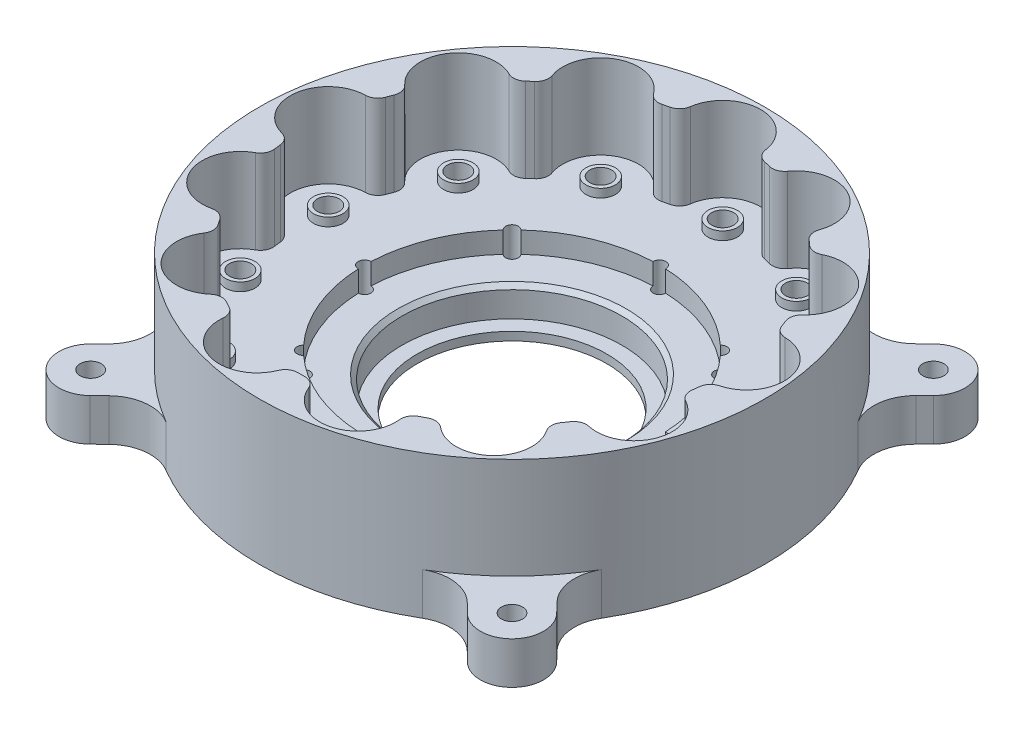
SolidWorks part; units mm, degrees
ref_plane "Front Plane" through (0, 0, 0) normal (0, 0, 1) x (1, 0, 0)
ref_plane "Top Plane" through (0, 0, 0) normal (0, 1, 0) x (1, 0, 0)
ref_plane "Right Plane" through (0, 0, 0) normal (1, 0, 0) x (0, 0, -1)
sketch "Sketch1" plane through (0, 0, 0) normal (0, 1, 0) x (1, 0, 0)
  circle A0 centre (0, 0) radius 60
  dimension "D1" = 120
extrude "Boss-Extrude1" add sketch "Sketch1" along normal blind 9
sketch "Sketch2" plane through (0, 9, 0) normal (0, 1, 0) x (1, 0, 0)
  circle A0 centre (0, 0) radius 26.1
  dimension "D1" = 52.2
extrude "Cut-Extrude1" cut sketch "Sketch2" against normal blind 7
sketch "Sketch3" plane through (0, 2, 0) normal (0, 1, 0) x (1, 0, 0)
  circle A0 centre (0, 0) radius 22.5
  dimension "D1" = 45
extrude "Cut-Extrude2" cut sketch "Sketch3" against normal blind 8
sketch "Sketch7" plane through (0, 9, 0) normal (0, 1, 0) x (1, 0, 0)
  circle A0 centre (0, 0) radius 35
  circle A1 centre (0, 0) radius 60 construction
  circle A2 centre (0, 0) radius 60
  dimension "D1" = 70
extrude "Boss-Extrude4" add sketch "Sketch7" along normal blind 5
sketch "Sketch4" plane through (0, 14, 0) normal (0, 1, 0) x (1, 0, 0)
  circle A0 centre (0, 50) radius 2.5
  circle A1 centre (23.2362, 44.2728) radius 2.5
  circle A2 centre (41.1492, 28.4032) radius 2.5
  circle A3 centre (49.6354, 6.0268) radius 2.5
  circle A4 centre (46.7508, -17.7302) radius 2.5
  circle A5 centre (33.1561, -37.4255) radius 2.5
  circle A6 centre (11.9658, -48.5471) radius 2.5
  circle A7 centre (-11.9658, -48.5471) radius 2.5
  circle A8 centre (-33.1561, -37.4255) radius 2.5
  circle A9 centre (-46.7508, -17.7302) radius 2.5
  circle A10 centre (-49.6354, 6.0268) radius 2.5
  circle A11 centre (-41.1492, 28.4032) radius 2.5
  circle A12 centre (-23.2362, 44.2728) radius 2.5
  point P30 (0, 0)
  dimension "5" = 5
  dimension "D1" = 50
  dimension "D3" = 13
extrude "Cut-Extrude3" cut sketch "Sketch4" against normal through all
sketch "Sketch5" plane through (0, 14, 0) normal (0, 1, 0) x (1, 0, 0)
  circle A0 centre (0, 50) radius 3.5
  circle A1 centre (0, 50) radius 2.5
  circle A2 centre (23.2362, 44.2728) radius 3.5
  circle A3 centre (23.2362, 44.2728) radius 2.5
  circle A4 centre (41.1492, 28.4032) radius 3.5
  circle A5 centre (41.1492, 28.4032) radius 2.5
  circle A6 centre (49.6354, 6.0268) radius 3.5
  circle A7 centre (49.6354, 6.0268) radius 2.5
  circle A8 centre (46.7508, -17.7302) radius 3.5
  circle A9 centre (46.7508, -17.7302) radius 2.5
  circle A10 centre (33.1561, -37.4255) radius 3.5
  circle A11 centre (33.1561, -37.4255) radius 2.5
  circle A12 centre (11.9658, -48.5471) radius 3.5
  circle A13 centre (11.9658, -48.5471) radius 2.5
  circle A14 centre (-11.9658, -48.5471) radius 3.5
  circle A15 centre (-11.9658, -48.5471) radius 2.5
  circle A16 centre (-33.1561, -37.4255) radius 3.5
  circle A17 centre (-33.1561, -37.4255) radius 2.5
  circle A18 centre (-46.7508, -17.7302) radius 3.5
  circle A19 centre (-46.7508, -17.7302) radius 2.5
  circle A20 centre (-49.6354, 6.0268) radius 3.5
  circle A21 centre (-49.6354, 6.0268) radius 2.5
  circle A22 centre (-41.1492, 28.4032) radius 3.5
  circle A23 centre (-41.1492, 28.4032) radius 2.5
  circle A24 centre (-23.2362, 44.2728) radius 3.5
  circle A25 centre (-23.2362, 44.2728) radius 2.5
  point P43 (0, 0)
  dimension "D1" = 7
  dimension "D2" = 5
  dimension "D3" = 13
extrude "Boss-Extrude2" add sketch "Sketch5" along normal blind 2
sketch "Sketch6" plane through (0, 14, 0) normal (0, 1, 0) x (1, 0, 0)
  arc A0 (8.9635, 49.19) -> (-8.9635, 49.19) centre (0, 50) ccw
  arc A2 (14.923, 47.7211) -> (8.9635, 49.19) centre (0, 0) ccw
  arc A3 (30.7965, 39.39) -> (14.923, 47.7211) centre (23.2362, 44.2728) ccw
  arc A4 (35.3907, 35.3199) -> (30.7965, 39.39) centre (0, 0) ccw
  arc A5 (45.5744, 20.5663) -> (35.3907, 35.3199) centre (41.1492, 28.4032) ccw
  arc A6 (47.7509, 14.8273) -> (45.5744, 20.5663) centre (0, 0) ccw
  arc A7 (49.9118, -2.9689) -> (47.7509, 14.8273) centre (49.6354, 6.0268) ccw
  arc A8 (49.1719, -9.062) -> (49.9118, -2.9689) centre (0, 0) ccw
  arc A9 (42.815, -25.824) -> (49.1719, -9.062) centre (46.7508, -17.7302) ccw
  arc A10 (39.3283, -30.8754) -> (42.815, -25.824) centre (0, 0) ccw
  arc A11 (25.9097, -42.7631) -> (39.3283, -30.8754) centre (33.1561, -37.4255) ccw
  arc A12 (20.475, -45.6155) -> (25.9097, -42.7631) centre (0, 0) ccw
  arc A13 (3.0689, -49.9057) -> (20.475, -45.6155) centre (11.9658, -48.5471) ccw
  arc A14 (-3.0689, -49.9057) -> (3.0689, -49.9057) centre (0, 0) ccw
  arc A15 (-20.475, -45.6155) -> (-3.0689, -49.9057) centre (-11.9658, -48.5471) ccw
  arc A16 (-25.9097, -42.7631) -> (-20.475, -45.6155) centre (0, 0) ccw
  arc A17 (-39.3283, -30.8754) -> (-25.9097, -42.7631) centre (-33.1561, -37.4255) ccw
  arc A18 (-42.815, -25.824) -> (-39.3283, -30.8754) centre (0, 0) ccw
  arc A19 (-49.1719, -9.062) -> (-42.815, -25.824) centre (-46.7508, -17.7302) ccw
  arc A20 (-49.9118, -2.9689) -> (-49.1719, -9.062) centre (0, 0) ccw
  arc A21 (-47.7509, 14.8273) -> (-49.9118, -2.9689) centre (-49.6354, 6.0268) ccw
  arc A22 (-45.5744, 20.5663) -> (-47.7509, 14.8273) centre (0, 0) ccw
  arc A23 (-35.3907, 35.3199) -> (-45.5744, 20.5663) centre (-41.1492, 28.4032) ccw
  arc A24 (-30.7965, 39.39) -> (-35.3907, 35.3199) centre (0, 0) ccw
  arc A25 (-14.923, 47.7211) -> (-30.7965, 39.39) centre (-23.2362, 44.2728) ccw
  arc A26 (-8.9635, 49.19) -> (-14.923, 47.7211) centre (0, 0) ccw
  circle A27 centre (0, 0) radius 60
  point P59 (0, 0)
  dimension "D1" = 18
  dimension "D2" = 13
  dimension "D3" = 120
extrude "Boss-Extrude3" add sketch "Sketch6" along normal blind 20
sketch "Sketch8" plane through (0, 0, 0) normal (0, -1, 0) x (1, 0, 0)
  circle A1 centre (23.2362, -44.2728) radius 2.6
  circle A2 centre (23.2362, -44.2728) radius 2.5
  circle A3 centre (23.2362, -44.2728) radius 2.5
  circle A4 centre (41.1492, -28.4032) radius 2.5
  circle A5 centre (41.1492, -28.4032) radius 2.5
  circle A6 centre (49.6354, -6.0268) radius 2.5
  circle A7 centre (49.6354, -6.0268) radius 2.5
  circle A8 centre (46.7508, 17.7302) radius 2.5
  circle A9 centre (46.7508, 17.7302) radius 2.5
  circle A10 centre (33.1561, 37.4255) radius 2.5
  circle A11 centre (33.1561, 37.4255) radius 2.5
  circle A12 centre (11.9658, 48.5471) radius 2.5
  circle A13 centre (11.9658, 48.5471) radius 2.5
  circle A14 centre (-11.9658, 48.5471) radius 2.5
  circle A15 centre (-11.9658, 48.5471) radius 2.5
  circle A16 centre (-33.1561, 37.4255) radius 2.5
  circle A17 centre (-33.1561, 37.4255) radius 2.5
  circle A18 centre (-46.7508, 17.7302) radius 2.5
  circle A19 centre (-46.7508, 17.7302) radius 2.5
  circle A20 centre (-49.6354, -6.0268) radius 2.5
  circle A21 centre (-49.6354, -6.0268) radius 2.5
  circle A22 centre (-41.1492, -28.4032) radius 2.5
  circle A23 centre (-41.1492, -28.4032) radius 2.5
  circle A24 centre (-23.2362, -44.2728) radius 2.5
  circle A25 centre (-23.2362, -44.2728) radius 2.5
  circle A26 centre (0, -50) radius 2.5
  circle A27 centre (0, -50) radius 2.5
  circle A28 centre (41.1492, -28.4032) radius 2.6
  circle A29 centre (49.6354, -6.0268) radius 2.6
  circle A30 centre (46.7508, 17.7302) radius 2.6
  circle A31 centre (33.1561, 37.4255) radius 2.6
  circle A32 centre (11.9658, 48.5471) radius 2.6
  circle A33 centre (-11.9658, 48.5471) radius 2.6
  circle A34 centre (-33.1561, 37.4255) radius 2.6
  circle A35 centre (-46.7508, 17.7302) radius 2.6
  circle A36 centre (-49.6354, -6.0268) radius 2.6
  circle A37 centre (-41.1492, -28.4032) radius 2.6
  circle A38 centre (-23.2362, -44.2728) radius 2.6
  circle A39 centre (0, -50) radius 2.6
  dimension "D1" = 0
  dimension "D2" = 0
  dimension "D3" = 0
  dimension "D4" = 0
  dimension "D5" = 0
  dimension "D6" = 0
  dimension "D7" = 0
  dimension "D8" = 0
  dimension "D9" = 0
  dimension "D10" = 0
  dimension "D11" = 0
  dimension "D12" = 0
  dimension "D13" = 0
  dimension "D14" = 0.1
extrude "Cut-Extrude4" cut sketch "Sketch8" along normal blind 8 from surface at -16 starting at face at (-11.9658, 16, 52.0471)
sketch "Sketch9" plane through (0, 0, 0) normal (0, -1, 0) x (-1, 0, 0)
  line L0 (-44.6967, -55.3033) -> (-42.6224, -53.229)
  line L1 (-55.3919, -44.7868) -> (-53.1382, -42.4558)
  line L2 (-55.3033, 44.6967) -> (-53.229, 42.6224)
  line L3 (-44.7868, 55.3919) -> (-42.4558, 53.1382)
  line L4 (44.6967, 55.3033) -> (42.6224, 53.229)
  line L5 (55.3919, 44.7868) -> (53.1382, 42.4558)
  line L6 (55.3033, -44.6967) -> (53.229, -42.6224)
  line L7 (44.7868, -55.3919) -> (42.4558, -53.1382)
  circle A0 centre (-50, -50) radius 2.5
  arc A1 (-55.3919, -44.7868) -> (-44.6967, -55.3033) centre (-50, -50) ccw
  arc A4 (-53.1382, -42.4558) -> (-51.7092, -30.4328) centre (-60.3274, -35.5049) ccw
  arc A5 (-42.6224, -53.229) -> (-30.4726, -51.6858) centre (-35.5514, -60.3001) cw
  circle A6 centre (0, 0) radius 60 construction
  arc A7 (-51.7092, -30.4328) -> (-30.4726, -51.6858) centre (0, 0) ccw
  arc A8 (-30.4328, 51.7092) -> (-51.6858, 30.4726) centre (0, 0) ccw
  arc A9 (-53.229, 42.6224) -> (-51.6858, 30.4726) centre (-60.3001, 35.5514) cw
  arc A10 (-44.7868, 55.3919) -> (-55.3033, 44.6967) centre (-50, 50) ccw
  arc A11 (-42.4558, 53.1382) -> (-30.4328, 51.7092) centre (-35.5049, 60.3274) ccw
  circle A12 centre (-50, 50) radius 2.5
  arc A13 (51.7092, 30.4328) -> (30.4726, 51.6858) centre (0, 0) ccw
  arc A14 (42.6224, 53.229) -> (30.4726, 51.6858) centre (35.5514, 60.3001) cw
  arc A15 (55.3919, 44.7868) -> (44.6967, 55.3033) centre (50, 50) ccw
  arc A16 (53.1382, 42.4558) -> (51.7092, 30.4328) centre (60.3274, 35.5049) ccw
  circle A17 centre (50, 50) radius 2.5
  arc A18 (30.4328, -51.7092) -> (51.6858, -30.4726) centre (0, 0) ccw
  arc A19 (53.229, -42.6224) -> (51.6858, -30.4726) centre (60.3001, -35.5514) cw
  arc A20 (44.7868, -55.3919) -> (55.3033, -44.6967) centre (50, -50) ccw
  arc A21 (42.4558, -53.1382) -> (30.4328, -51.7092) centre (35.5049, -60.3274) ccw
  circle A22 centre (50, -50) radius 2.5
  point P46 (0, 0)
  dimension "D3" = 5
  dimension "D4" = 15
  dimension "D5" = 10
  dimension "D1" = 50
  dimension "D2" = 50
  dimension "D6" = 4
extrude "Boss-Extrude5" add sketch "Sketch9" against normal blind 10
sketch "Sketch10" plane through (0, 0, 0) normal (0, -1, 0) x (-1, 0, 0)
  circle A0 centre (35, 0) radius 1.5
  circle A1 centre (24.7487, -24.7487) radius 1.5
  circle A2 centre (0, -35) radius 1.5
  circle A3 centre (-24.7487, -24.7487) radius 1.5
  circle A4 centre (-35, 0) radius 1.5
  circle A5 centre (-24.7487, 24.7487) radius 1.5
  circle A6 centre (0, 35) radius 1.5
  circle A7 centre (24.7487, 24.7487) radius 1.5
  point P19 (0, 0)
  dimension "D2" = 3
  dimension "D1" = 35
  dimension "D3" = 8
extrude "Cut-Extrude5" cut sketch "Sketch10" against normal through all
chamfer "Chamfer1" distance 1 angle 45 1 edges at (0, 9, 26.1)
fillet "Fillet1" radius 3 26 edges at (20.475, 24, 45.6155) (25.9097, 24, 42.7631) (-45.5744, 24, -20.5663) (-47.7509, 24, -14.8273) (-49.9118, 24, 2.9689) (-49.1719, 24, 9.062) (-35.3907, 24, -35.3199) (-30.7965, 24, -39.39) (-14.923, 24, -47.7211) (-8.9635, 24, -49.19) (8.9635, 24, -49.19) (14.923, 24, -47.7211) (30.7965, 24, -39.39) (35.3907, 24, -35.3199) (45.5744, 24, -20.5663) (47.7509, 24, -14.8273) (49.9118, 24, 2.9689) (49.1719, 24, 9.062) (42.815, 24, 25.824) (39.3283, 24, 30.8754) (-42.815, 24, 25.824) (-39.3283, 24, 30.8754) (-25.9097, 24, 42.7631) (-20.475, 24, 45.6155) (-3.0689, 24, 49.9057) (3.0689, 24, 49.9057)
